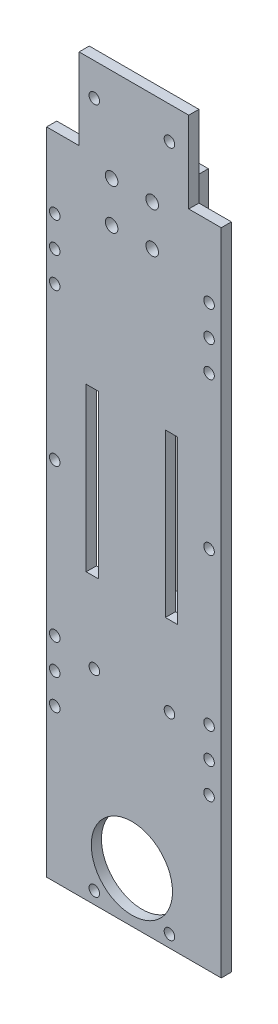
SolidWorks part; units mm, degrees
ref_plane "前视基准面" through (0, 0, 0) normal (0, 0, 1) x (1, 0, 0)
ref_plane "上视基准面" through (0, 0, 0) normal (0, 1, 0) x (1, 0, 0)
ref_plane "右视基准面" through (0, 0, 0) normal (1, 0, 0) x (0, 0, -1)
sketch "草图1" plane through (0, 0, 0) normal (0, 0, 1) x (1, 0, 0)
  line L0 (0, 0) -> (0, 90) construction
  line L1 (0, 0) -> (0, -90) construction
  line L2 (22, 70) -> (14, 70)
  line L3 (0.5, 70) -> (-5, 70)
  line L4 (22, -90) -> (22, 70)
  line L5 (22, -90) -> (16, -90)
  line L6 (-21, -90) -> (-21, 70)
  line L7 (11.25, 20) -> (8.25, 20)
  line L8 (11.25, -20) -> (8.25, -20)
  line L9 (2.5, 90) -> (2.5, -90) construction
  line L10 (2.5, -90) -> (-2.5, -90)
  line L11 (-2.5, -90) -> (-2.5, 90) construction
  line L12 (-8.25, -20) -> (-11.25, -20)
  line L13 (-16, 90) -> (-16, -90) construction
  line L14 (-5, 70) -> (-5, 67) construction
  line L15 (16, 90) -> (16, -90) construction
  line L16 (-5, 67) -> (5, 67) construction
  line L17 (5, 67) -> (5, 57) construction
  line L18 (16, -90) -> (2.5, -90)
  line L19 (5, 57) -> (-5, 57) construction
  line L20 (9.25, -90) -> (9.25, -87) construction
  line L21 (-9.25, -90) -> (-9.25, -87) construction
  line L22 (-19, -45) -> (-19, -37.5) construction
  line L23 (-19, -45) -> (-19, -52.5) construction
  line L24 (19, -45) -> (19, -37.5) construction
  line L25 (19, -45) -> (19, -52.5) construction
  line L26 (-8.25, 20) -> (-11.25, 20)
  line L27 (19, 45) -> (19, 52.5) construction
  line L28 (-19, 45) -> (-19, 52.5) construction
  line L29 (19, 45) -> (19, 37.5) construction
  line L30 (0, -39.7148) -> (-9.25, -39.7148) construction
  line L31 (0, -39.7148) -> (9.25, -39.7148) construction
  line L32 (11.25, 20) -> (11.25, -20)
  line L33 (0, 82) -> (-9.25, 82) construction
  line L34 (-11.25, -20) -> (-11.25, 20)
  line L35 (-19, 45) -> (-19, 37.5) construction
  line L36 (0, 82) -> (9.25, 82) construction
  line L37 (8.25, 20) -> (8.25, -20)
  line L38 (-8.25, 20) -> (-8.25, -20)
  line L39 (-2.5, -90) -> (-16, -90)
  line L40 (-16, -90) -> (-21, -90)
  line L41 (14, 70) -> (14, 90)
  line L42 (-21, 70) -> (-13, 70)
  line L43 (-13, 70) -> (-13, 90)
  line L44 (-13, 90) -> (14, 90)
  circle A0 centre (-19, 0) radius 1.3
  circle A1 centre (19, 0) radius 1.3
  circle A2 centre (-19, 45) radius 1.3
  circle A3 centre (19, 45) radius 1.3
  circle A4 centre (19, -45) radius 1.3
  circle A5 centre (-19, -45) radius 1.3
  circle A6 centre (5, 67) radius 1.55
  circle A7 centre (-5, 67) radius 1.55
  circle A8 centre (-5, 57) radius 1.55
  circle A9 centre (5, 57) radius 1.55
  circle A10 centre (0, -77.616) radius 10
  circle A11 centre (9.25, -87) radius 1.3
  circle A12 centre (-9.25, -87) radius 1.3
  circle A13 centre (9.25, -39.7148) radius 1.3
  circle A14 centre (-9.25, -39.7148) radius 1.3
  circle A15 centre (-19, -52.5) radius 1.3
  circle A16 centre (-19, -37.5) radius 1.3
  circle A17 centre (19, -37.5) radius 1.3
  circle A18 centre (19, -52.5) radius 1.3
  circle A19 centre (19, 37.5) radius 1.3
  circle A20 centre (19, 52.5) radius 1.3
  circle A21 centre (-19, 52.5) radius 1.3
  circle A22 centre (-19, 37.5) radius 1.3
  circle A23 centre (9.25, 82) radius 1.3
  circle A24 centre (-9.25, 82) radius 1.3
extrude "凸台-拉伸1" add sketch "草图1" along normal blind 2.5
sketch "草图2" plane through (0, 0, 0) normal (0, 0, -1) x (-1, 0, 0)
  line L0 (-2.325, -52.5) -> (1.675, -52.5)
  line L1 (-2.325, 52.5) -> (-0.325, 52.5)
  line L2 (-0.325, 52.5) -> (1.675, 52.5)
  line L3 (-12.325, 24) -> (-12.325, 20.5)
  line L4 (-2.325, 32.5) -> (-2.325, -52.5)
  line L5 (-2.325, 20) -> (-2.325, 24)
  line L6 (-2.325, 24) -> (-12.325, 24)
  line L7 (1.675, 32.5) -> (1.675, -52.5)
  line L8 (-12.325, 20.5) -> (11.675, 20.5)
  line L9 (11.675, 20.5) -> (11.675, 24)
  line L10 (1.675, 24) -> (11.675, 24)
  line L11 (-11.25, -25) -> (-11.25, -21.5)
  line L12 (-11.25, -21.5) -> (11.25, -21.5)
  line L13 (11.25, -21.5) -> (11.25, -25)
  line L14 (-2.325, 32.5) -> (-2.325, 52.5)
  line L15 (1.675, 32.5) -> (1.675, 52.5)
  line L16 (1.675, -52.5) -> (11.25, -52.5)
  line L17 (11.25, -25) -> (-11.25, -25)
  line L18 (11.25, -52.5) -> (11.25, -56)
  line L19 (1.675, 52.5) -> (9.675, 52.5)
  line L20 (-2.325, 52.5) -> (-10.325, 52.5)
  line L21 (-10.325, 52.5) -> (-10.325, 72.5)
  line L22 (-10.325, 72.5) -> (9.675, 72.5)
  line L23 (9.675, 72.5) -> (9.675, 52.5)
  line L24 (-10.325, 52.5) -> (-10.325, 24)
  line L25 (-10.325, 24) -> (-7.325, 24)
  line L26 (-7.325, 24) -> (-7.325, 52.5)
  line L27 (9.675, 52.5) -> (9.675, 24)
  line L28 (6.675, 24) -> (6.675, 52.5)
  line L29 (11.25, -56) -> (-11.25, -56)
  line L30 (-11.25, -56) -> (-11.25, -52.5)
  line L31 (-11.25, -52.5) -> (-2.325, -52.5)
  circle A0 centre (-5, 67) radius 1.55
  circle A1 centre (5, 67) radius 1.55
  circle A2 centre (5, 57) radius 1.55
  circle A3 centre (-5, 57) radius 1.55
  circle M19 centre (-5, 57) radius 1.55
  circle M20 centre (5, 57) radius 1.55
  circle M21 centre (5, 67) radius 1.55
  circle M22 centre (-5, 67) radius 1.55
extrude "凸台-拉伸2" add sketch "草图2" along normal blind 6 contours L23 L22 L21 L20 L1 L2 L19 M19 M21 M22 M20 | L28 L10 L27 L19 | L7 L15 L2 L1 L14 L4 L8 | L6 L26 L20 L24 | L3 L8 L4 L6 | L10 L7 L8 L9 | L4 L12 L7 L8 L5 | L7 L17 L4 L0 | L17 L13 L12 L7 | L17 L7 L12 L4 | L17 L4 L12 L11 | L31 L30 L29 L18 L16 L0
